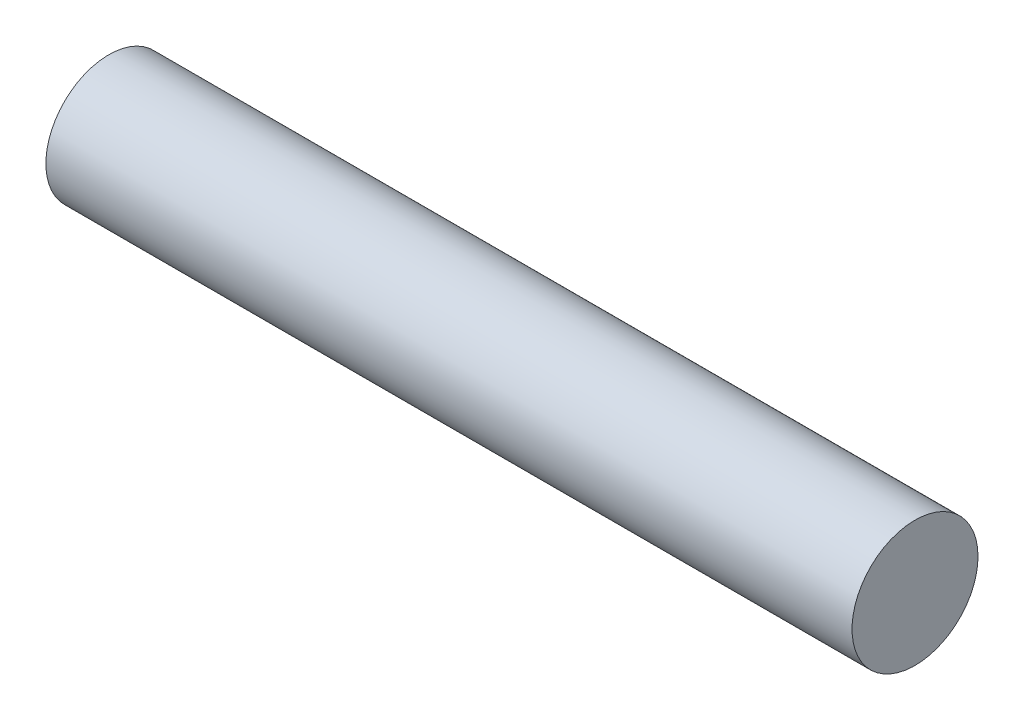
SolidWorks part; units mm, degrees
ref_plane "Front Plane" through (0, 0, 0) normal (0, 0, 1) x (1, 0, 0)
ref_plane "Top Plane" through (0, 0, 0) normal (0, 1, 0) x (1, 0, 0)
ref_plane "Right Plane" through (0, 0, 0) normal (1, 0, 0) x (0, 0, -1)
sketch "Sketch1" plane through (0, 0, 0) normal (1, 0, 0) x (0, 0, -1)
  circle A0 centre (0, 0) radius 1.5875
  dimension "D1" = 3.175
extrude "Boss-Extrude1" add sketch "Sketch1" along normal blind 20.32
